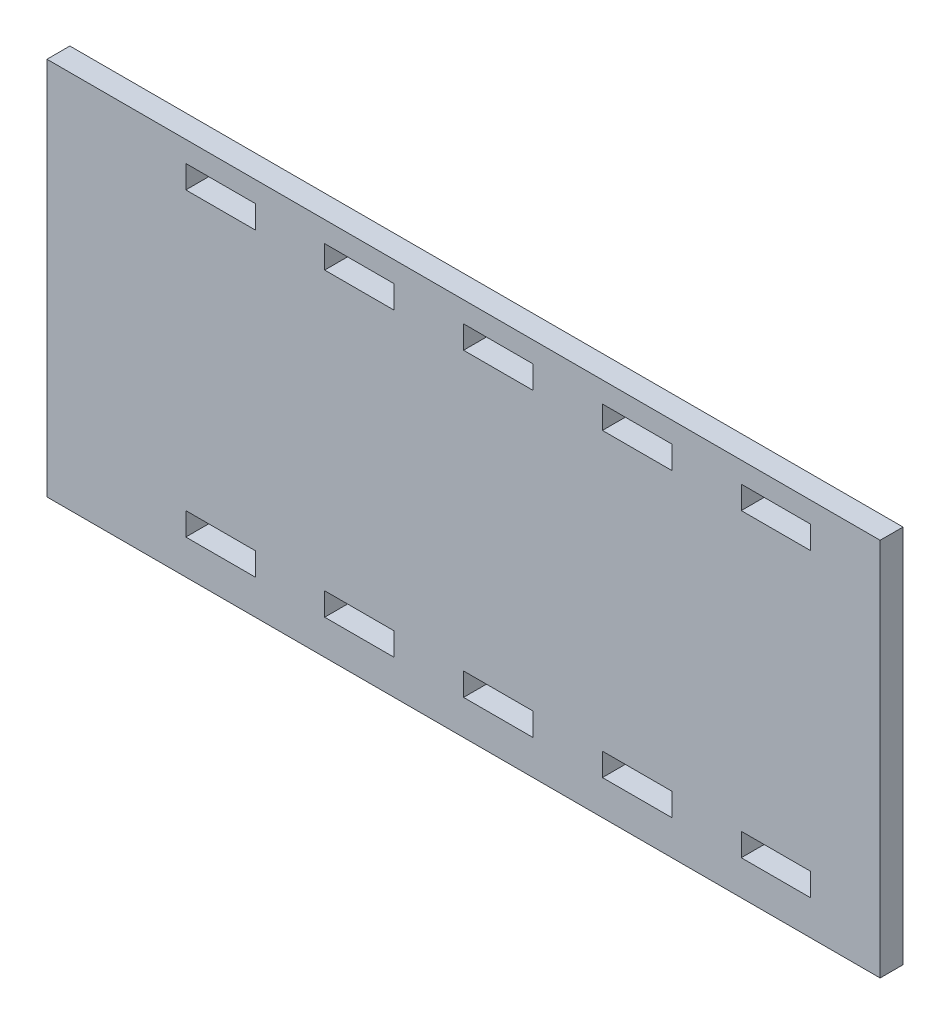
SolidWorks part; units mm, degrees
ref_plane "Front Plane" through (0, 0, 0) normal (0, 0, 1) x (1, 0, 0)
ref_plane "Top Plane" through (0, 0, 0) normal (0, 1, 0) x (1, 0, 0)
ref_plane "Right Plane" through (0, 0, 0) normal (1, 0, 0) x (0, 0, -1)
sketch "Sketch1" plane through (0, 0, 0) normal (0, 0, 1) x (1, 0, 0)
  line L1 (-60, 60) -> (60, 60)
  line L2 (-60, 60) -> (-60, -60)
  line L3 (-60, -60) -> (60, -60)
  line L4 (60, 60) -> (60, -60)
  line L5 (-60, 60) -> (60, -60) construction
  line L6 (-60, -60) -> (60, 60) construction
  point P0 (0, 0)
  dimension "D1" = 120
  dimension "D2" = 120
extrude "Boss-Extrude1" add sketch "Sketch1" along normal blind 3.3
sketch "Sketch2" plane through (0, 0, 3.3) normal (0, 0, 1) x (1, 0, 0)
  line L0 (60, -60) -> (60, 60) construction
  line L1 (50, -16.7) -> (40, -16.7)
  line L2 (50, -16.7) -> (50, -20)
  line L3 (50, -20) -> (40, -20)
  line L4 (40, -16.7) -> (40, -20)
  line L5 (-60, -60) -> (60, -60) construction
  line L7 (40, 23.3) -> (50, 23.3)
  line L8 (40, 23.3) -> (40, 26.6)
  line L9 (40, 26.6) -> (50, 26.6)
  line L10 (50, 23.3) -> (50, 26.6)
  dimension "D1" = 10
  dimension "D2" = 10
  dimension "D3" = 3.3
  dimension "D4" = 40
  dimension "D5" = 40
  dimension "D6" = 3.3
  dimension "D7" = 10
extrude "Cut-Extrude1" cut sketch "Sketch2" against normal blind 3.3
pattern_linear "LPattern1" count 5 spacing 20 along (-1, 0, 0) of "Cut-Extrude1"
sketch "Sketch3" plane through (0, 0, 0) normal (0, 0, -1) x (-1, 0, 0)
  line L0 (60, 60) -> (60, -60) construction
  line L1 (-60, 60) -> (60, 60)
  line L2 (-60, 60) -> (-60, 29.6)
  line L3 (-60, 29.6) -> (60, 29.6)
  line L4 (60, 60) -> (60, 29.6)
  line L5 (-50, 26.6) -> (-40, 26.6) construction
  dimension "D1" = 3
extrude "Cut-Extrude2" cut sketch "Sketch3" against normal blind 3.3
sketch "Sketch4" plane through (0, -60, 0) normal (0, -1, 0) x (1, 0, 0)
  line L1 (-60, 3.3) -> (60, 3.3)
  line L2 (-60, 3.3) -> (-60, 0)
  line L3 (-60, 0) -> (60, 0)
  line L4 (60, 3.3) -> (60, 0)
extrude "Cut-Extrude3" cut sketch "Sketch4" against normal blind 35
